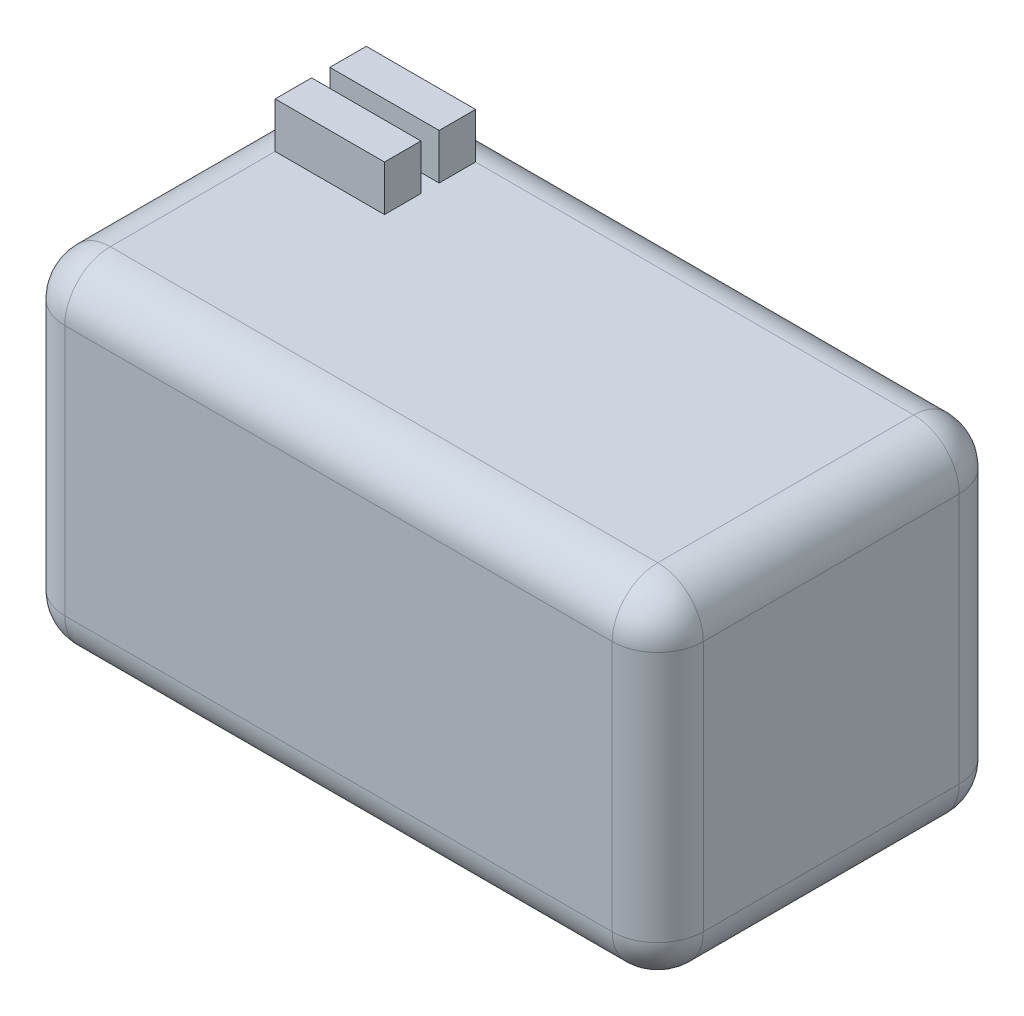
SolidWorks part; units mm, degrees
ref_plane "Front Plane" through (0, 0, 0) normal (0, 0, 1) x (1, 0, 0)
ref_plane "Top Plane" through (0, 0, 0) normal (0, 1, 0) x (1, 0, 0)
ref_plane "Right Plane" through (0, 0, 0) normal (1, 0, 0) x (0, 0, -1)
sketch "Sketch1" plane through (0, 0, 0) normal (0, 0, 1) x (1, 0, 0)
  line L0 (-28.9728, 26.0643) -> (-28.9728, -11.5257)
  line L1 (-28.9728, -11.5257) -> (41.1272, -11.5257)
  line L2 (41.1272, -11.5257) -> (41.1272, 26.0643)
  line L3 (41.1272, 26.0643) -> (-28.9728, 26.0643)
  dimension "D1" = 70.1
  dimension "D2" = 37.59
extrude "Boss-Extrude1" add sketch "Sketch1" along normal blind 38.1
fillet "Fillet1" radius 5 12 edges at (41.1272, 7.2693, 38.1) (6.0772, -11.5257, 38.1) (-28.9728, 7.2693, 38.1) (6.0772, 26.0643, 38.1) (-28.9728, 7.2693, 0) (6.0772, -11.5257, 0) (6.0772, 26.0643, 0) (-28.9728, -11.5257, 19.05) (-28.9728, 26.0643, 19.05) (41.1272, 7.2693, 0) (41.1272, 26.0643, 19.05) (41.1272, -11.5257, 19.05)
sketch "Sketch2" plane through (0, 26.0643, 0) normal (0, 1, 0) x (1, 0, 0)
  line L0 (-23.9728, -5) -> (-23.9728, -15)
  line L1 (-23.9728, -5) -> (-23.9728, -33.1) construction
  line L2 (-23.9728, -15) -> (-11.9728, -15)
  line L3 (-11.9728, -15) -> (-11.9728, -5)
  line L4 (36.1272, -5) -> (-23.9728, -5) construction
  line L5 (-11.9728, -5) -> (-23.9728, -5)
  line L6 (-11.9728, -9) -> (-23.9728, -9)
  line L7 (-23.9728, -11) -> (-11.9728, -11)
  line M7 (36.1272, -5) -> (-23.9728, -5)
  line M8 (-23.9728, -5) -> (-23.9728, -33.1)
  dimension "D1" = 12
  dimension "D2" = 10
  dimension "D3" = 4
  dimension "D4" = 4
extrude "Boss-Extrude2" add sketch "Sketch2" along normal blind 5 contours L7 L2 L3 M8 | L6 L3 M7 M8
